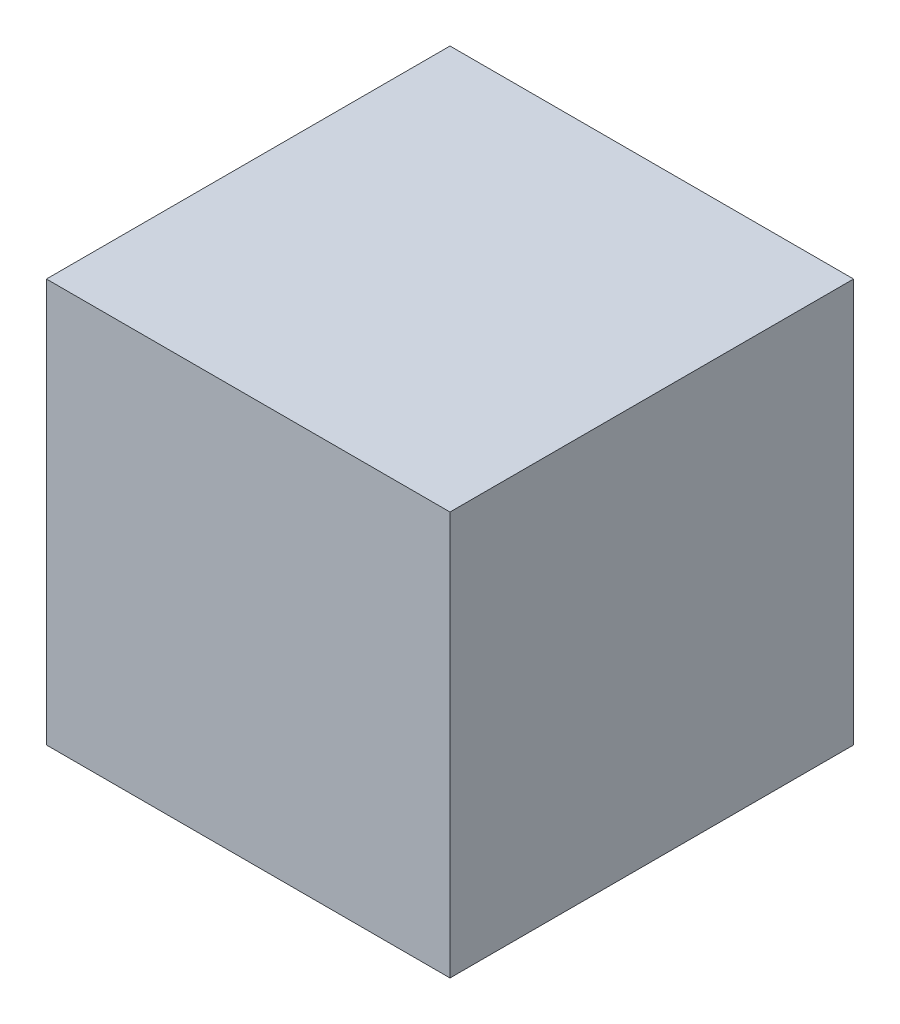
SolidWorks part; units mm, degrees
ref_plane "Front Plane" through (0, 0, 0) normal (0, 0, 1) x (1, 0, 0)
ref_plane "Top Plane" through (0, 0, 0) normal (0, 1, 0) x (1, 0, 0)
ref_plane "Right Plane" through (0, 0, 0) normal (1, 0, 0) x (0, 0, -1)
sketch "Sketch2" plane through (0, 0, 0) normal (0, 1, 0) x (1, 0, 0)
  line L1 (-15.875, -15.875) -> (15.875, -15.875)
  line L2 (-15.875, -15.875) -> (-15.875, 15.875)
  line L3 (-15.875, 15.875) -> (15.875, 15.875)
  line L4 (15.875, -15.875) -> (15.875, 15.875)
  line L5 (-15.875, -15.875) -> (15.875, 15.875) construction
  line L6 (-15.875, 15.875) -> (15.875, -15.875) construction
  point P0 (0, 0)
  dimension "D1" = 31.75
  dimension "D2" = 31.75
extrude "Boss-Extrude1" add sketch "Sketch2" along normal blind 31.75
